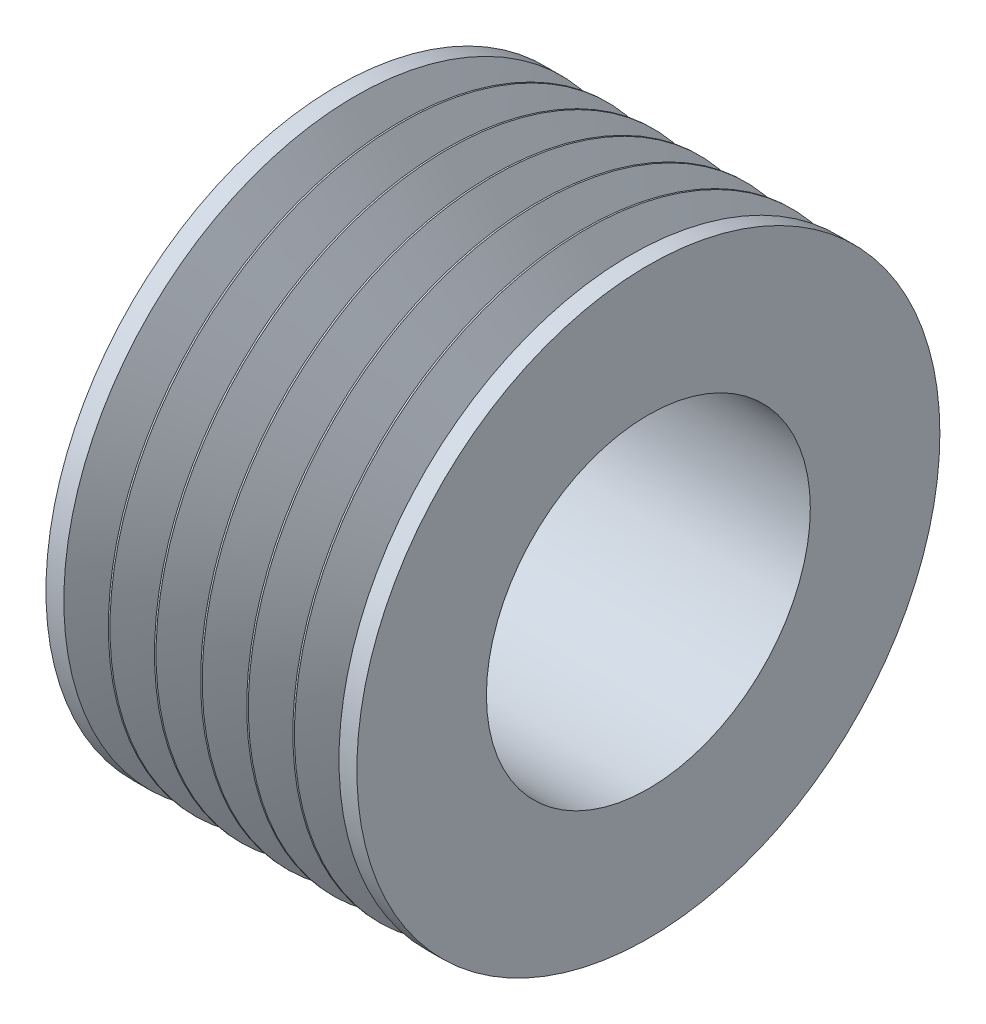
SolidWorks part; units mm, degrees
material "AISI 1020"
ref_plane "Спереди" through (0, 0, 0) normal (0, 0, 1) x (1, 0, 0)
ref_plane "Сверху" through (0, 0, 0) normal (0, 1, 0) x (1, 0, 0)
ref_plane "Справа" through (0, 0, 0) normal (1, 0, 0) x (0, 0, -1)
sketch "Эскиз1" plane through (0, 0, 0) normal (0, 0, 1) x (1, 0, 0)
  line L0 (63.7549, 0) -> (-85.5502, 0) construction
  line L1 (0, 12.5) -> (-23.9957, 12.5)
  line L2 (0, 22.5) -> (0, 12.5)
  line L4 (0, 22.5) -> (-1.38, 22.5)
  line L5 (-23.9957, 22.5) -> (-23.9957, 12.5)
  line L11 (-1.38, 22.5) -> (-2.9205, 19.5408)
  line L12 (-3.2753, 19.5408) -> (-4.8157, 22.5)
  line L13 (-6.8353, 19.5408) -> (-8.3757, 22.5)
  line L14 (-4.94, 22.5) -> (-6.4805, 19.5408)
  line L15 (-10.3953, 19.5408) -> (-11.9357, 22.5)
  line L16 (-8.5, 22.5) -> (-10.0405, 19.5408)
  line L17 (-13.9553, 19.5408) -> (-15.4957, 22.5)
  line L18 (-12.06, 22.5) -> (-13.6005, 19.5408)
  line L19 (-17.5153, 19.5408) -> (-19.0557, 22.5)
  line L20 (-15.62, 22.5) -> (-17.1605, 19.5408)
  line L21 (-21.0753, 19.5408) -> (-22.6157, 22.5)
  line L22 (-19.18, 22.5) -> (-20.7205, 19.5408)
  line L23 (-22.6157, 22.5) -> (-23.9957, 22.5)
  line L24 (-19.0557, 22.5) -> (-19.18, 22.5)
  line L25 (-15.4957, 22.5) -> (-15.62, 22.5)
  line L26 (-11.9357, 22.5) -> (-12.06, 22.5)
  line L27 (-8.3757, 22.5) -> (-8.5, 22.5)
  line L28 (-4.8157, 22.5) -> (-4.94, 22.5)
  arc A0 (-2.9205, 19.5408) -> (-3.2753, 19.5408) centre (-3.0979, 19.6331) cw
  arc A1 (-6.4805, 19.5408) -> (-6.8353, 19.5408) centre (-6.6579, 19.6331) cw
  arc A2 (-10.0405, 19.5408) -> (-10.3953, 19.5408) centre (-10.2179, 19.6331) cw
  arc A3 (-13.6005, 19.5408) -> (-13.9553, 19.5408) centre (-13.7779, 19.6331) cw
  arc A4 (-17.1605, 19.5408) -> (-17.5153, 19.5408) centre (-17.3379, 19.6331) cw
  arc A5 (-20.7205, 19.5408) -> (-21.0753, 19.5408) centre (-20.8979, 19.6331) cw
  point P33 (-3.0979, 19.2)
  dimension "D13" = 0.2
  dimension "D14" = 0.1243
  dimension "D15" = 3.56
  dimension "D2" = 1.38
  dimension "D3" = 45
  dimension "D4" = 25
  dimension "D5" = 23.9957
  dimension "D10" = 55
  dimension "D12" = 3.3
  dimension "D16" = 3.0979
  dimension "D11" = 6
revolve "Повернуть1" add sketch "Эскиз1" angle 360 about L0
ref_plane "Плоскость1" through (-11.9979, 0, 0) normal (-1, 0, 0) x (0, 0, 1)
